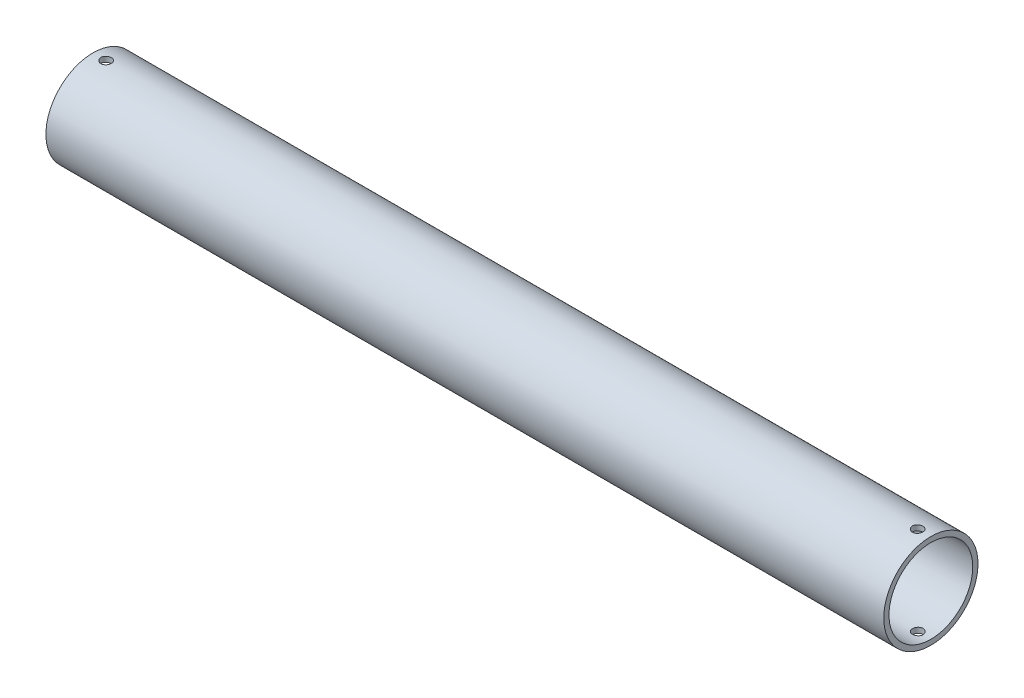
SolidWorks part; units mm, degrees
ref_plane "Front Plane" through (0, 0, 0) normal (0, 0, 1) x (1, 0, 0)
ref_plane "Top Plane" through (0, 0, 0) normal (0, 1, 0) x (1, 0, 0)
ref_plane "Right Plane" through (0, 0, 0) normal (1, 0, 0) x (0, 0, -1)
sketch "Sketch1" plane through (0, 0, 0) normal (1, 0, 0) x (0, 0, -1)
  circle A0 centre (0, 0) radius 28.575
  circle A1 centre (0, 0) radius 25.4
  dimension "D1" = 50.8
  dimension "D2" = 57.15
extrude "Boss-Extrude1" add sketch "Sketch1" along normal blind 508
sketch "Sketch2" plane through (0, 0, 0) normal (0, 1, 0) x (1, 0, 0)
  line L0 (254, 28.575) -> (254, -93.0466) construction
  line L1 (508, 28.575) -> (0, 28.575) construction
  line L2 (0, 28.575) -> (0, -28.575) construction
  circle A0 centre (7.9764, 0) radius 3.175
  circle A1 centre (500.0236, 0) radius 3.175
  dimension "D1" = 6.35
  dimension "D2" = 7.9764
extrude "Cut-Extrude1" cut sketch "Sketch2" against normal through all both and the other way through all
ref_plane "Plane1" through (0, 28.575, 0) normal (0, 1, 0) x (1, 0, 0)
